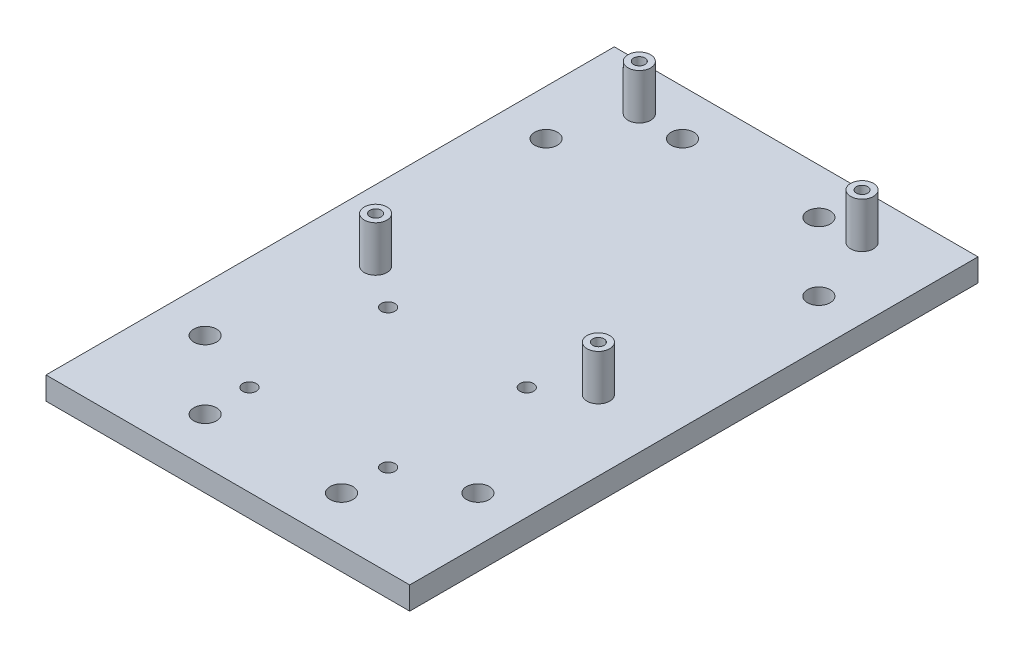
SolidWorks part; units mm, degrees
ref_plane "Front Plane" through (0, 0, 0) normal (0, 0, 1) x (1, 0, 0)
ref_plane "Top Plane" through (0, 0, 0) normal (0, 1, 0) x (1, 0, 0)
ref_plane "Right Plane" through (0, 0, 0) normal (1, 0, 0) x (0, 0, -1)
sketch "Sketch1" plane through (0, 0, 0) normal (0, 1, 0) x (1, 0, 0)
  line L0 (-1000, 0) -> (49000, 0) construction
  line L5 (-40, -62.5) -> (40, -62.5)
  line L6 (-40, -62.5) -> (-40, 62.5)
  line L7 (-40, 62.5) -> (40, 62.5)
  line L8 (40, -62.5) -> (40, 62.5)
  line L9 (-40, -62.5) -> (40, 62.5) construction
  line L10 (-40, 62.5) -> (40, -62.5) construction
  line L11 (0, -1000) -> (0, 49000) construction
  line L12 (0, 62.5) -> (0, 52.5) construction
  line L13 (-24.5, 52.5) -> (24.5, 52.5) construction
  line L14 (24.5, 52.5) -> (24.5, -5.5) construction
  line L15 (-975.5, -5.5) -> (49024.5, -5.5) construction
  line L16 (0, -5.5) -> (0, -15.5) construction
  line L17 (-1000, -15.5) -> (49000, -15.5) construction
  line L18 (0, -62.5) -> (0, -42.5) construction
  line L19 (-15.25, -42.5) -> (15.25, -42.5) construction
  line L20 (-15.25, -42.5) -> (-15.25, -12) construction
  line L21 (15.25, -42.5) -> (15.25, -12) construction
  line L22 (-40, 62.5) -> (-25, 62.5) construction
  circle A0 centre (-24.5, 52.5) radius 1.25
  circle A1 centre (24.5, 52.5) radius 1.25
  circle A2 centre (-24.5, -5.5) radius 1.25
  circle A3 centre (24.5, -5.5) radius 1.25
  circle A4 centre (-15.25, -12) radius 1.5
  circle A5 centre (15.25, -12) radius 1.5
  circle A6 centre (-15.25, -42.5) radius 1.5
  circle A7 centre (15.25, -42.5) radius 1.5
  point P0 (40, 62.5)
  point P1 (0, 0)
  point P15 (-24.5, -5.5)
  point P20 (0, 52.5)
  point P36 (0, -42.5)
  point P41 (-98.1815, 48.0552)
  point P42 (0, 0)
  point P43 (0, 0)
  dimension "D1" = 30.5
  dimension "D2" = 30.5
  dimension "D3" = 30.5
extrude "Boss-Extrude1" add sketch "Sketch1" along normal blind 5
sketch "Sketch2" plane through (0, 5, 0) normal (0, 1, 0) x (1, 0, 0)
  line L0 (-40, 62.5) -> (-15, 62.5) construction
  line L1 (40, 62.5) -> (-40, 62.5) construction
  line L2 (-40, 62.5) -> (-40, 37.5) construction
  line L3 (-40, 62.5) -> (-40, -62.5) construction
  line L4 (-15, 62.5) -> (-15, 52.5) construction
  line L5 (-40, 37.5) -> (-30, 37.5) construction
  line L6 (-1000, 0) -> (49000, 0) construction
  line L7 (0, -1000) -> (0, 49000) construction
  circle A0 centre (-15, 52.5) radius 2.5
  circle A1 centre (-30, 37.5) radius 2.5
  circle A2 centre (15, 52.5) radius 2.5
  circle A3 centre (30, 37.5) radius 2.5
  circle A4 centre (30, -37.5) radius 2.5
  circle A5 centre (15, -52.5) radius 2.5
  circle A6 centre (-15, -52.5) radius 2.5
  circle A7 centre (-30, -37.5) radius 2.5
extrude "Cut-Extrude1" cut sketch "Sketch2" against normal blind 5
sketch "Sketch3" plane through (0, 5, 0) normal (0, 1, 0) x (1, 0, 0)
  circle A0 centre (-24.5, 52.5) radius 2.5
  circle A1 centre (24.5, 52.5) radius 2.5
  circle A2 centre (-24.5, -5.5) radius 2.5
  circle A3 centre (24.5, -5.5) radius 2.5
  circle A4 centre (-24.5, 52.5) radius 1.25
  circle A5 centre (24.5, 52.5) radius 1.25
  circle A6 centre (24.5, -5.5) radius 1.25
  circle A7 centre (-24.5, -5.5) radius 1.25
  point P0 (-24.5, 52.5)
  point P1 (24.5, 52.5)
  point P3 (24.5, -5.5)
  point P5 (-24.5, -5.5)
extrude "Boss-Extrude2" add sketch "Sketch3" along normal blind 10
